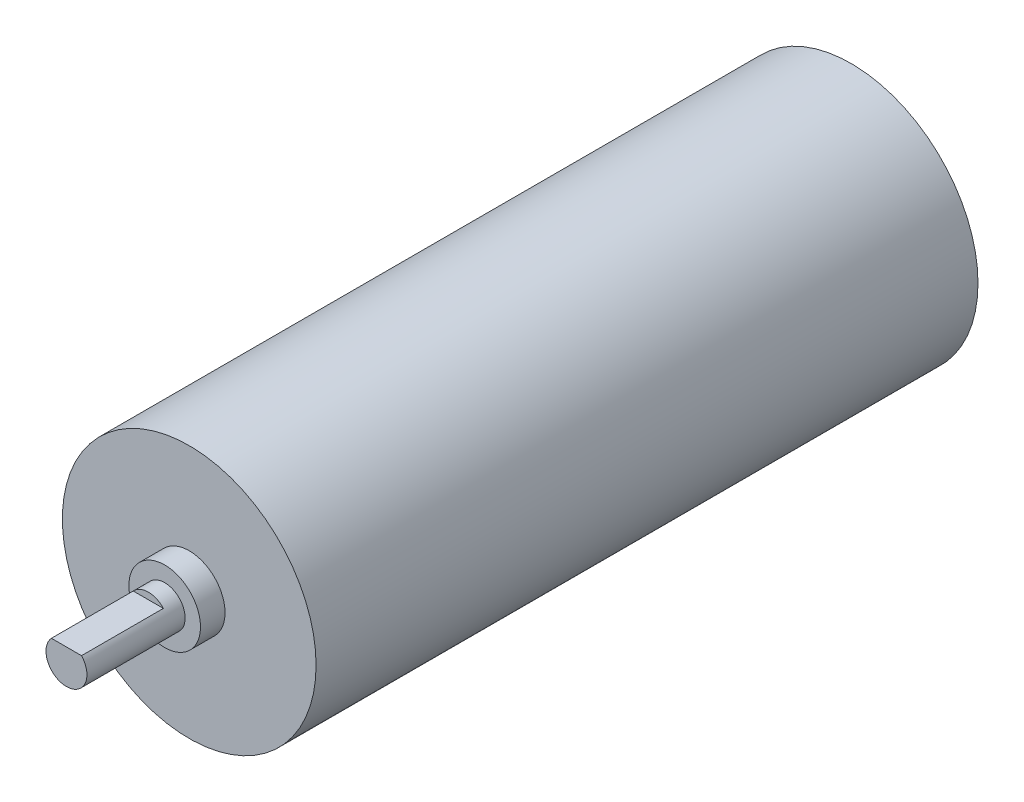
SolidWorks part; units mm, degrees
ref_plane "Front Plane" through (0, 0, 0) normal (0, 0, 1) x (1, 0, 0)
ref_plane "Top Plane" through (0, 0, 0) normal (0, 1, 0) x (1, 0, 0)
ref_plane "Right Plane" through (0, 0, 0) normal (1, 0, 0) x (0, 0, -1)
sketch "Sketch1" plane through (0, 0, 0) normal (0, 0, 1) x (1, 0, 0)
  circle A0 centre (0, 0) radius 12.4
  dimension "D1" = 24.8
extrude "Main Extrude" add sketch "Sketch1" along normal blind 64.7
sketch "Sketch2" plane through (0, 0, 64.7) normal (0, 0, 1) x (1, 0, 0)
  circle A0 centre (0, 0) radius 3.5
extrude "Boss-Extrude2" add sketch "Sketch2" along normal blind 2.4
sketch "Sketch3" plane through (0, 0, 67.1) normal (0, 0, 1) x (1, 0, 0)
  circle A0 centre (0, 0) radius 2
extrude "Boss-Extrude3" add sketch "Sketch3" along normal blind 9.6
sketch "Sketch5" plane through (0, 0, 76.7) normal (0, 0, 1) x (1, 0, 0)
  line L0 (-1.4721, 1.3539) -> (1.4721, 1.3539)
  arc A0 (1.4721, 1.3539) -> (-1.4721, 1.3539) centre (0, 0) ccw
extrude "Key Cut" cut sketch "Sketch5" against normal blind 8
